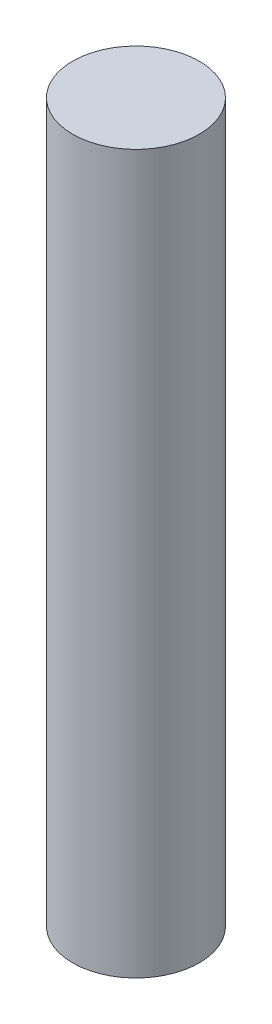
SolidWorks part; units mm, degrees
material "AISI 1020"
ref_plane "Front Plane" through (0, 0, 0) normal (0, 0, 1) x (1, 0, 0)
ref_plane "Top Plane" through (0, 0, 0) normal (0, 1, 0) x (1, 0, 0)
ref_plane "Right Plane" through (0, 0, 0) normal (1, 0, 0) x (0, 0, -1)
sketch "Sketch1" plane through (0, 0, 0) normal (0, 1, 0) x (1, 0, 0)
  circle A0 centre (0, 0) radius 1.5
  dimension "D1" = 3
extrude "Boss-Extrude1" add sketch "Sketch1" along normal blind 17
